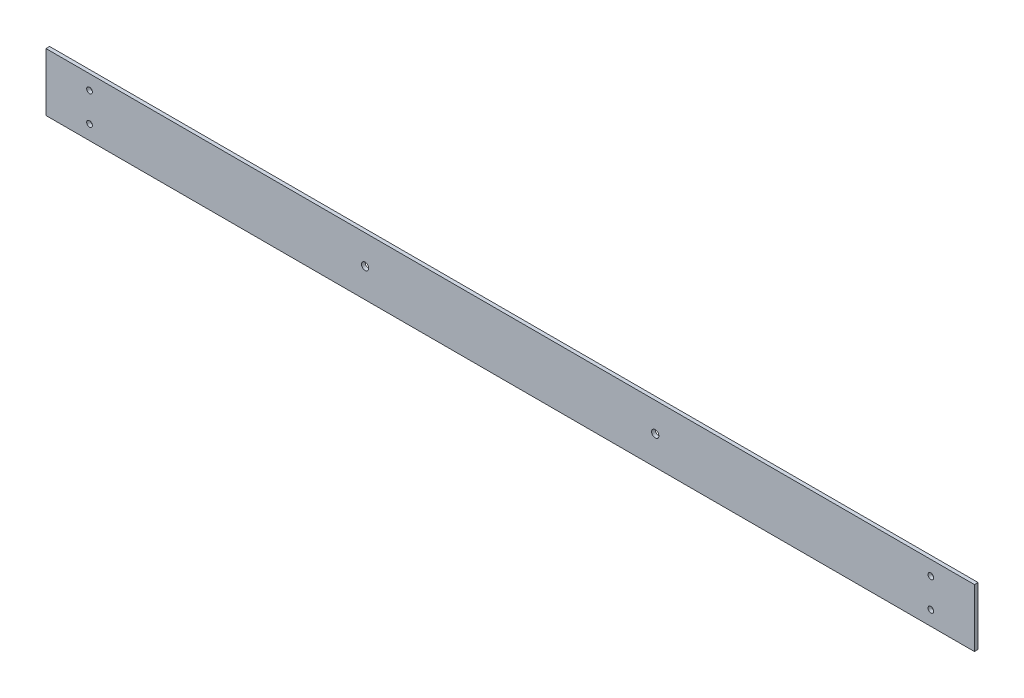
SolidWorks part; units mm, degrees
ref_plane "Front" through (0, 0, 0) normal (0, 0, 1) x (1, 0, 0)
ref_plane "Top" through (0, 0, 0) normal (0, 1, 0) x (1, 0, 0)
ref_plane "Right" through (0, 0, 0) normal (1, 0, 0) x (0, 0, -1)
sketch "Sketch1" plane through (0, 0, 0) normal (0, 0, 1) x (1, 0, 0)
  line L1 (0, 0) -> (812.8, 0)
  line L2 (0, 0) -> (0, 50.8)
  line L3 (0, 50.8) -> (812.8, 50.8)
  line L4 (812.8, 0) -> (812.8, 50.8)
  dimension "D1" = 50.8
  dimension "D2" = 812.8
extrude "Boss-Extrude1" add sketch "Sketch1" along normal blind 3.175
sketch "Sketch2" plane through (0, 0, 0) normal (0, 0, -1) x (-1, 0, 0)
  line L0 (-812.8, 25.4) -> (0, 25.4) construction
  line L1 (-812.8, 0) -> (-812.8, 50.8) construction
  line L2 (0, 50.8) -> (0, 0) construction
  line L3 (-774.7, 0) -> (-774.7, 50.8) construction
  line L4 (0, 0) -> (-812.8, 0) construction
  line L5 (-812.8, 50.8) -> (0, 50.8) construction
  line L6 (-38.1, 0) -> (-38.1, 50.8) construction
  circle A0 centre (-533.4, 25.4) radius 3.175
  circle A1 centre (-279.4, 25.4) radius 3.175
  circle A2 centre (-38.1, 12.7) radius 2.4892
  circle A3 centre (-38.1, 38.1) radius 2.4892
  circle A4 centre (-774.7, 12.7) radius 2.4892
  circle A5 centre (-774.7, 38.1) radius 2.4892
  dimension "D1" = 6.35
  dimension "D6" = 4.9784
  dimension "D3" = 279.4
  dimension "D4" = 279.4
  dimension "D2" = 38.1
  dimension "D5" = 38.1
  dimension "D7" = 12.7
  dimension "D8" = 25.4
extrude "Cut-Extrude1" cut sketch "Sketch2" against normal through all
equation "\"D4@Sketch2\"=\"D3@Sketch2\""
equation "\"D2@Sketch2\"=\"D5@Sketch2\""
